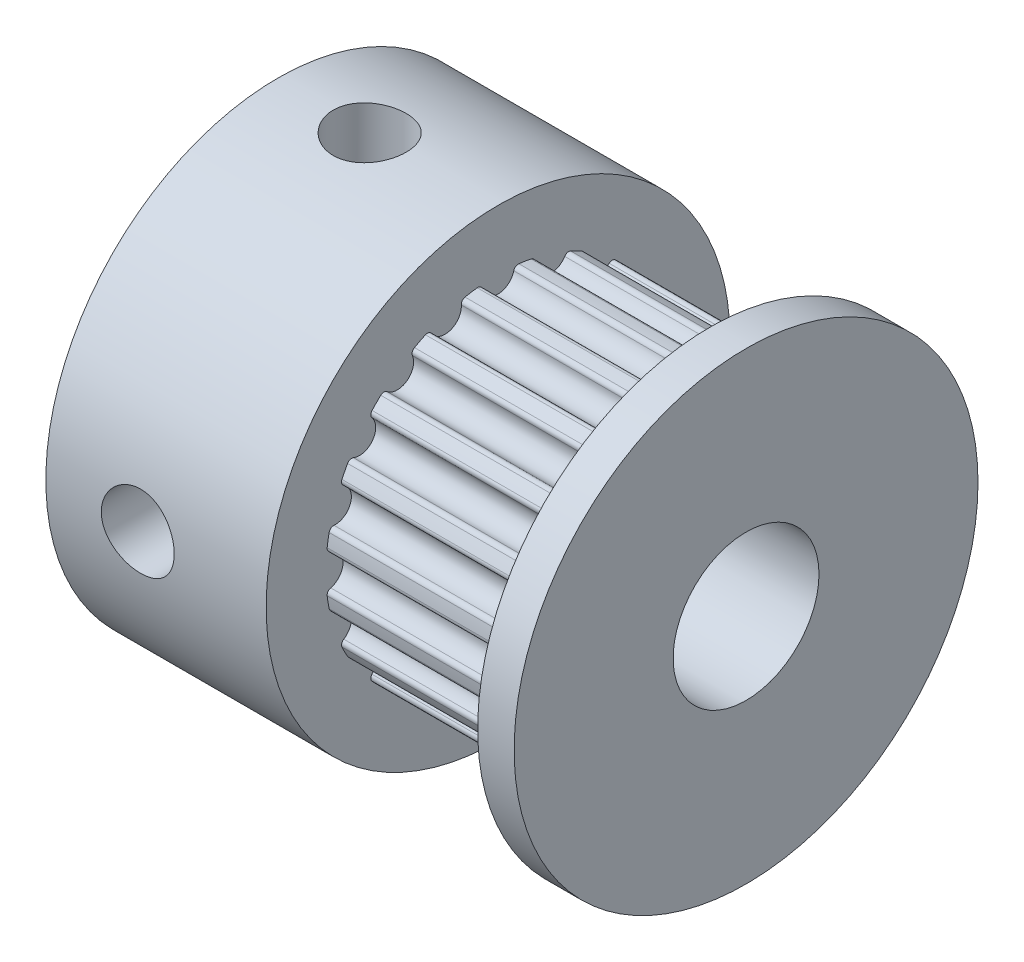
SolidWorks part; units mm, degrees
material "6061-T6 (SS)"
ref_plane "Front Plane" through (0, 0, 0) normal (0, 0, 1) x (1, 0, 0)
ref_plane "Top Plane" through (0, 0, 0) normal (0, 1, 0) x (1, 0, 0)
ref_plane "Right Plane" through (0, 0, 0) normal (1, 0, 0) x (0, 0, -1)
sketch "Sketch1" plane through (0, 0, 0) normal (0, 0, 1) x (1, 0, 0)
  line L1 (0, 7.95) -> (7.55, 7.95)
  line L2 (7.55, 7.95) -> (7.55, 5.9)
  line L3 (7.55, 5.9) -> (14.8, 5.9)
  line L4 (14.8, 5.9) -> (14.8, 7.95)
  line L5 (14.8, 7.95) -> (16.05, 7.95)
  line L6 (16.05, 7.95) -> (16.05, 2.5)
  line L7 (16.05, 2.5) -> (0, 2.5)
  line L8 (0, 0) -> (-7.6744, 0) construction
  line L9 (0, 7.95) -> (0, 2.5)
  dimension "D1" = 5
  dimension "D2" = 15.9
  dimension "D3" = 11.8
  dimension "D4" = 16.05
  dimension "D5" = 7.25
  dimension "D6" = 1.25
revolve "Revolve1" add sketch "Sketch1" angle 360 about L8
sketch "Croquis5" plane through (14.8, 0, 0) normal (-1, 0, 0) x (0, 0, 1)
  line L0 (0, 0) -> (0, 5.87) construction
  circle A0 centre (0, 5.87) radius 0.555
  circle A1 centre (1.8139, 5.5827) radius 0.555
  circle A2 centre (3.4503, 4.7489) radius 0.555
  circle A3 centre (4.7489, 3.4503) radius 0.555
  circle A4 centre (5.5827, 1.8139) radius 0.555
  circle A5 centre (5.87, 0) radius 0.555
  circle A6 centre (5.5827, -1.8139) radius 0.555
  circle A7 centre (4.7489, -3.4503) radius 0.555
  circle A8 centre (3.4503, -4.7489) radius 0.555
  circle A9 centre (1.8139, -5.5827) radius 0.555
  circle A10 centre (0, -5.87) radius 0.555
  circle A11 centre (-1.8139, -5.5827) radius 0.555
  circle A12 centre (-3.4503, -4.7489) radius 0.555
  circle A13 centre (-4.7489, -3.4503) radius 0.555
  circle A14 centre (-5.5827, -1.8139) radius 0.555
  circle A15 centre (-5.87, 0) radius 0.555
  circle A16 centre (-5.5827, 1.8139) radius 0.555
  circle A17 centre (-4.7489, 3.4503) radius 0.555
  circle A18 centre (-3.4503, 4.7489) radius 0.555
  circle A19 centre (-1.8139, 5.5827) radius 0.555
  dimension "D1" = 1.11
  dimension "D2" = 20
  dimension "D3" = 5.87
extrude "Cortar-Extruir1" cut sketch "Croquis5" along normal up to surface (7.25 mm away) up to face at (7.55, 0, -7.95)
fillet "Redondeo1" radius 0.16 40 edges at (11.175, 5.8738, -0.555) (11.175, 5.8738, 0.555) (11.175, 5.7579, 1.2873) (11.175, 5.4149, 2.3429) (11.175, 5.0782, 3.0036) (11.175, 4.4258, 3.9015) (11.175, 3.9015, 4.4258) (11.175, 3.0036, 5.0782) (11.175, 2.3429, 5.4149) (11.175, 1.2873, 5.7579) (11.175, 0.555, 5.8738) (11.175, -0.555, 5.8738) (11.175, -1.2873, 5.7579) (11.175, -2.3429, 5.4149) (11.175, -3.0036, 5.0782) (11.175, -3.9015, 4.4258) (11.175, -4.4258, 3.9015) (11.175, -5.0782, 3.0036) (11.175, -5.4149, 2.3429) (11.175, -5.7579, 1.2873) (11.175, -5.8738, 0.555) (11.175, -5.8738, -0.555) (11.175, -5.7579, -1.2873) (11.175, -5.4149, -2.3429) (11.175, -5.0782, -3.0036) (11.175, -4.4258, -3.9015) (11.175, -3.9015, -4.4258) (11.175, -3.0036, -5.0782) (11.175, -2.3429, -5.4149) (11.175, -1.2873, -5.7579) (11.175, -0.555, -5.8738) (11.175, 0.555, -5.8738) (11.175, 1.2873, -5.7579) (11.175, 2.3429, -5.4149) (11.175, 3.0036, -5.0782) (11.175, 3.9015, -4.4258) (11.175, 4.4258, -3.9015) (11.175, 5.0782, -3.0036) (11.175, 5.4149, -2.3429) (11.175, 5.7579, -1.2873)
hole_wizard "M3x0.5 Tapped Hole1" positions "Sketch3" profile "Sketch2" tap size "M3x0.5" standard "ANSI Metric"
sketch "Sketch3" plane through (0, 0, 0) normal (0, 1, 0) x (1, 0, 0)
  line L0 (0, 0) -> (6.3, 0) construction
  point P8 (3.15, 0)
sketch "Sketch2" plane through (3.15, 0, 0) normal (1, 0, 0) x (0, 0, -1)
  line L0 (0, 0) -> (0, 7.95)
  line L1 (0, 7.95) -> (1.25, 7.95)
  line L2 (1.25, 7.95) -> (1.25, 0)
  line L5 (1.25, 0) -> (0, 0)
  line L11 (0, -6.35) -> (0, 107.95) construction
  dimension "Thread Major Dia." = 2.5
  dimension "Thru Tap Drill Depth" = 7.95
hole_wizard "M3x0.5 Tapped Hole2" positions "Sketch5" profile "Sketch4" tap size "M3x0.5" standard "ANSI Metric"
sketch "Sketch5" plane through (0, 0, 0) normal (0, 0, 1) x (1, 0, 0)
  line L0 (0, 0) -> (6.3, 0) construction
  point P7 (3.15, 0)
sketch "Sketch4" plane through (3.15, 0, 0) normal (1, 0, 0) x (0, 1, 0)
  line L0 (0, 0) -> (0, 7.95)
  line L1 (0, 7.95) -> (1.25, 7.95)
  line L2 (1.25, 7.95) -> (1.25, 0)
  line L5 (1.25, 0) -> (0, 0)
  line L11 (0, -6.35) -> (0, 107.95) construction
  dimension "Thread Major Dia." = 2.5
  dimension "Thru Tap Drill Depth" = 7.95
ref_plane "Plano1" through (11.175, 0, 0) normal (1, 0, 0) x (0, 0, -1)
